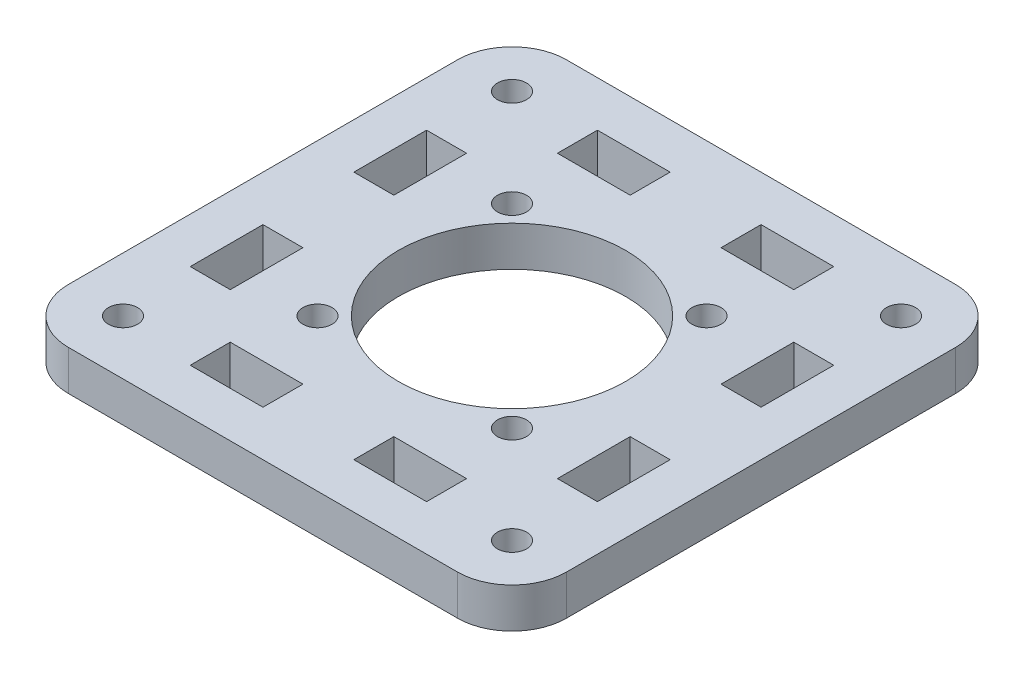
SolidWorks part; units mm, degrees
ref_plane "前视基准面" through (0, 0, 0) normal (0, 0, 1) x (1, 0, 0)
ref_plane "上视基准面" through (0, 0, 0) normal (0, 1, 0) x (1, 0, 0)
ref_plane "右视基准面" through (0, 0, 0) normal (1, 0, 0) x (0, 0, -1)
sketch "草图1" plane through (0, 0, 0) normal (0, 1, 0) x (1, 0, 0)
  line L0 (0, 0) -> (27.4, 27.4) construction
  line L1 (-27.4, 27.4) -> (27.4, 27.4)
  line L2 (-27.4, 27.4) -> (-27.4, -27.4)
  line L3 (-27.4, -27.4) -> (27.4, -27.4)
  line L4 (27.4, 27.4) -> (27.4, -27.4)
  line L5 (0, -27.4) -> (0, 27.4) construction
  line L6 (-27.4, 0) -> (27.4, 0) construction
  line L7 (18, -5) -> (18, 5) construction
  line L8 (18, 5) -> (22.4, 5)
  line L9 (22.4, 5) -> (22.4, -5) construction
  line L10 (18, 5) -> (18, 13)
  line L11 (18, 13) -> (22.4, 13)
  line L12 (22.4, 13) -> (22.4, 5)
  line L13 (0, 0) -> (27.4, -27.4) construction
  line L14 (22.4, -13) -> (22.4, -5)
  line L15 (18, -13) -> (22.4, -13)
  line L16 (18, -5) -> (18, -13)
  line L17 (18, -5) -> (22.4, -5)
  line L18 (-22.4, 5) -> (-22.4, -5) construction
  line L19 (-18, -5) -> (-18, 5) construction
  line L20 (-18, -5) -> (-22.4, -5)
  line L21 (-18, -5) -> (-18, -13)
  line L22 (-18, -13) -> (-22.4, -13)
  line L23 (-22.4, -13) -> (-22.4, -5)
  line L24 (-22.4, 13) -> (-22.4, 5)
  line L25 (-18, 13) -> (-22.4, 13)
  line L26 (-18, 5) -> (-18, 13)
  line L27 (-18, 5) -> (-22.4, 5)
  line L28 (0, 0) -> (-27.4, -27.4) construction
  line L29 (0, 0) -> (-27.4, 27.4) construction
  line L30 (13, 22.4) -> (5, 22.4)
  line L31 (13, 18) -> (13, 22.4)
  line L32 (5, 18) -> (13, 18)
  line L33 (5, 18) -> (5, 22.4)
  line L34 (5, -18) -> (5, -22.4)
  line L35 (5, -18) -> (13, -18)
  line L36 (13, -18) -> (13, -22.4)
  line L37 (13, -22.4) -> (5, -22.4)
  line L38 (-13, -22.4) -> (-5, -22.4)
  line L39 (-13, -18) -> (-13, -22.4)
  line L40 (-5, -18) -> (-13, -18)
  line L41 (-5, -18) -> (-5, -22.4)
  line L42 (-5, 18) -> (-5, 22.4)
  line L43 (-5, 18) -> (-13, 18)
  line L44 (-13, 18) -> (-13, 22.4)
  line L45 (-13, 22.4) -> (-5, 22.4)
  line L46 (18, 13) -> (18, 18) construction
  circle A0 centre (0, 0) radius 12.5
  circle A1 centre (21.4, 21.4) radius 1.6
  circle A2 centre (21.4, -21.4) radius 1.6
  circle A3 centre (-21.4, -21.4) radius 1.6
  circle A4 centre (-21.4, 21.4) radius 1.6
  point P17 (22.4, 0)
  point P18 (18, 0)
  point P32 (-18, 0)
  point P33 (-22.4, 0)
  dimension "D1" = 25
  dimension "D8" = 3.2
  dimension "D2" = 45
  dimension "D3" = 4.4
  dimension "D4" = 18
  dimension "D5" = 10
  dimension "D6" = 8
  dimension "D7" = 5
  dimension "D9" = 6
extrude "凸台-拉伸1" add sketch "草图1" along normal blind 4.4
fillet "圆角1" radius 6 4 edges at (-27.4, 2.2, 27.4) (-27.4, 2.2, -27.4) (27.4, 2.2, -27.4) (27.4, 2.2, 27.4)
sketch "草图2" plane through (0, 4.4, 0) normal (0, 1, 0) x (1, 0, 0)
  line L0 (0, 0) -> (21.4, 21.4) construction
  line L1 (0, 0) -> (21.4, -21.4) construction
  line L2 (0, 0) -> (-21.4, -21.4) construction
  line L3 (0, 0) -> (-21.4, 21.4) construction
  circle A0 centre (10.7, 10.7) radius 1.6
  circle A1 centre (10.7, -10.7) radius 1.6
  circle A2 centre (-10.7, -10.7) radius 1.6
  circle A3 centre (-10.7, 10.7) radius 1.6
  point P17 (0, 0)
  dimension "D1" = 3.2
  dimension "D2" = 4
extrude "切除-拉伸1" cut sketch "草图2" against normal blind 10
